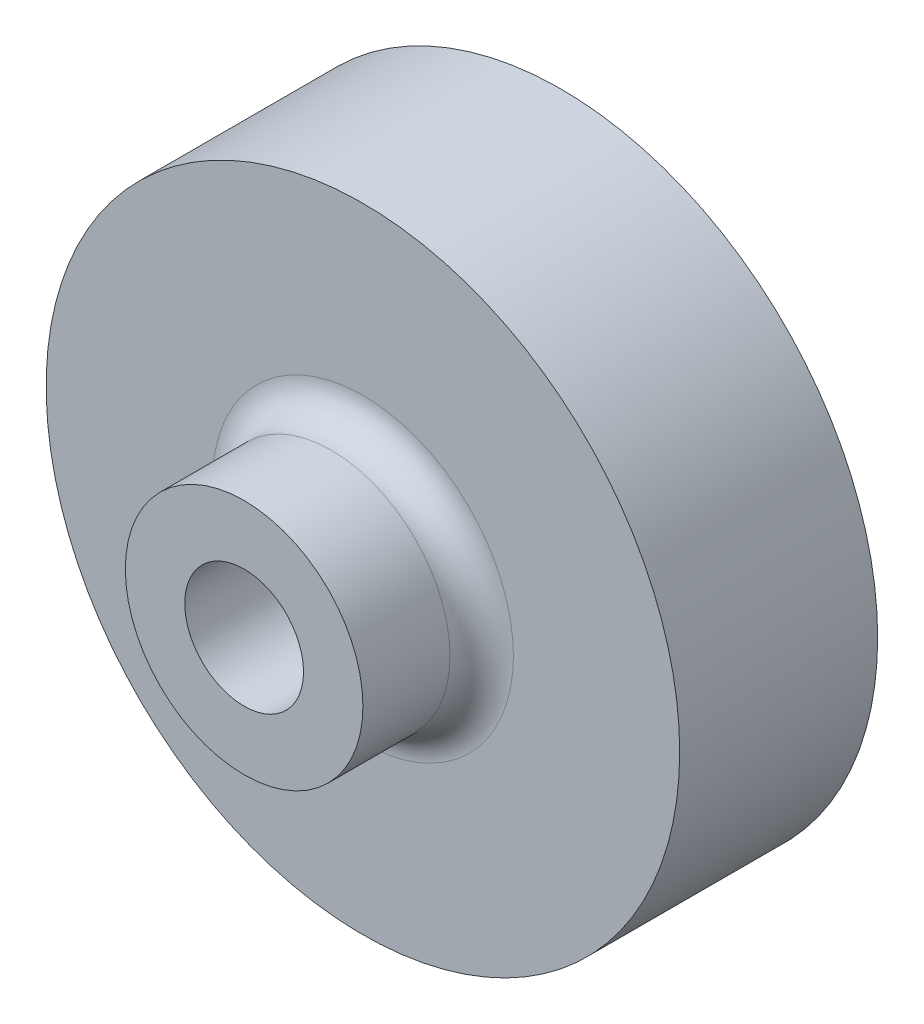
SolidWorks part; units mm, degrees
ref_plane "Front Plane" through (0, 0, 0) normal (0, 0, 1) x (1, 0, 0)
ref_plane "Top Plane" through (0, 0, 0) normal (0, 1, 0) x (1, 0, 0)
ref_plane "Right Plane" through (0, 0, 0) normal (1, 0, 0) x (0, 0, -1)
sketch "Sketch1" plane through (0, 0, 0) normal (0, 1, 0) x (1, 0, 0)
  line L1 (0, 0) -> (3.75, 0)
  line L2 (0, 0) -> (0, 3.75)
  line L3 (0, 3.75) -> (3.75, 3.75)
  line L4 (3.75, 0) -> (3.75, 3.75)
  line L5 (0, 3.75) -> (10, 3.75)
  line L6 (0, 3.75) -> (0, 10)
  line L7 (0, 10) -> (10, 10)
  line L8 (10, 3.75) -> (10, 10)
  dimension "D1" = 3.75
  dimension "D2" = 3.75
  dimension "D3" = 6.25
  dimension "D4" = 10
revolve "Revolve1" add sketch "Sketch1" angle 360 about L6
sketch "Sketch2" plane through (0, 0, -10) normal (0, 0, -1) x (-1, 0, 0)
  line L0 (0.5, 1.8071) -> (0.5, -1.8071)
  line L1 (0, 55) -> (0, -55) construction
  line L2 (-0.5, 1.8071) -> (-0.5, -1.8071)
  arc A1 (0.5, 1.8071) -> (0.5, -1.8071) centre (0, 0) cw
  arc A2 (-0.5, 1.8071) -> (-0.5, -1.8071) centre (0, 0) ccw
  point P3 (1.875, 0)
  dimension "D1" = 0.5
  dimension "D2" = 1.875
extrude "Cut-Extrude1" cut sketch "Sketch2" against normal blind 1.25
fillet "Fillet1" radius 1 1 edges at (3.75, 0, -3.75)
sketch "Sketch3" plane through (0, 0, 0) normal (0, 0, 1) x (1, 0, 0)
  circle A0 centre (0, 0) radius 1.875
  dimension "D1" = 3.75
extrude "Cut-Extrude2" cut sketch "Sketch3" against normal blind 8.75
